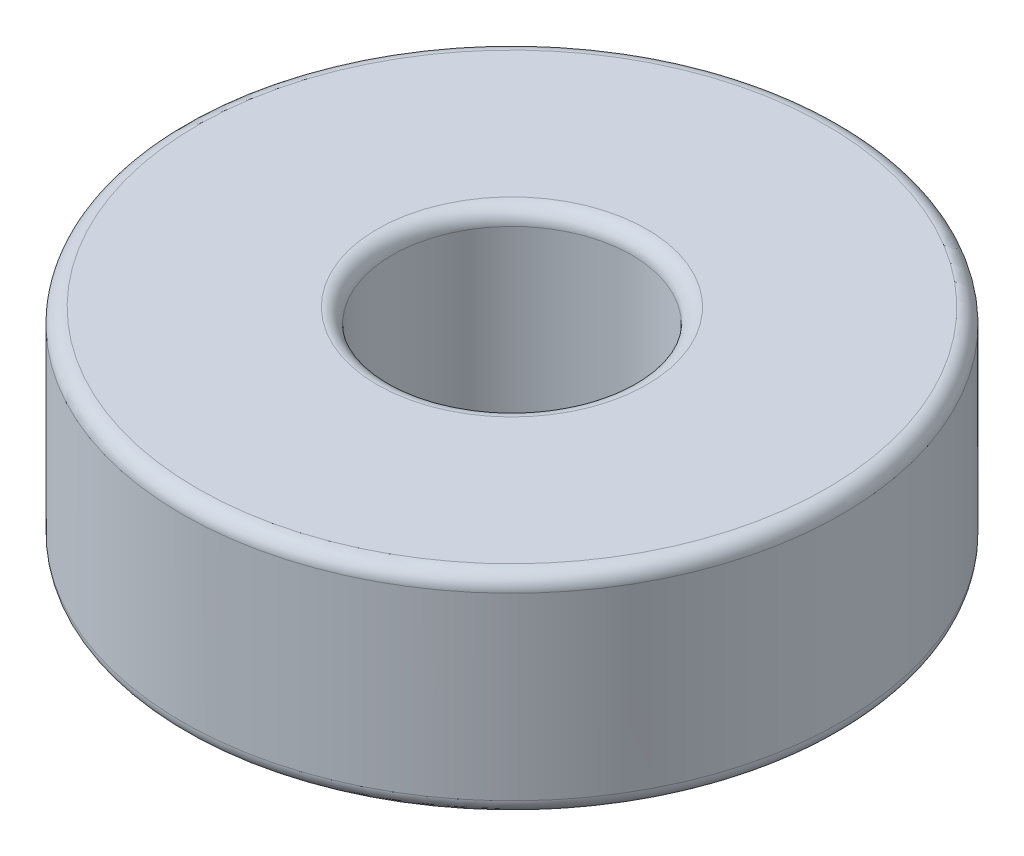
SolidWorks part; units mm, degrees
ref_plane "Face" through (0, 0, 0) normal (0, 0, 1) x (1, 0, 0)
ref_plane "Dessus" through (0, 0, 0) normal (0, 1, 0) x (1, 0, 0)
ref_plane "Droite" through (0, 0, 0) normal (1, 0, 0) x (0, 0, -1)
sketch "Esquisse1" plane through (0, 0, 0) normal (0, 0, 1) x (1, 0, 0)
  line L0 (0, 0) -> (0, 7) construction
  line L2 (4, 0) -> (11, 0)
  line L3 (4, 0) -> (4, 7)
  line L4 (4, 7) -> (11, 7)
  line L5 (11, 0) -> (11, 7)
  dimension "D1" = 8
  dimension "D2" = 22
  dimension "D3" = 7
revolve "Révolution1" add sketch "Esquisse1" angle 360 about L0
fillet "Congé1" radius 0.5 4 edges at (0, 0, -4) (0, 0, -11) (0, 7, -11) (0, 7, -4)
